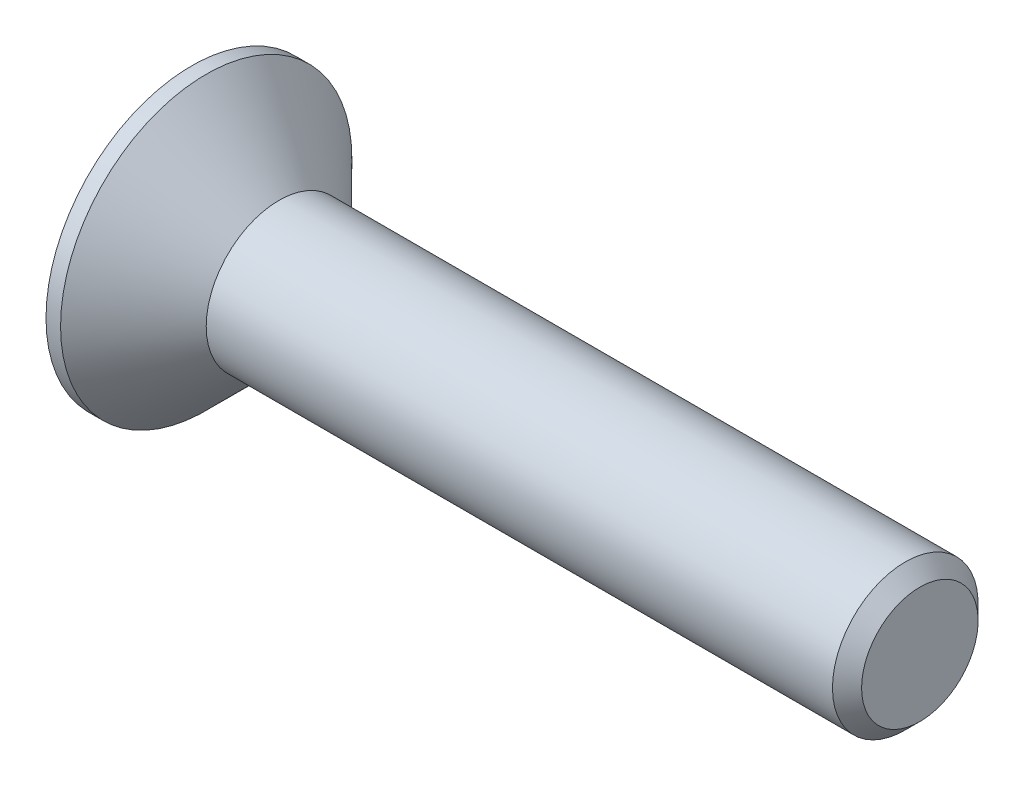
SolidWorks part; units mm, degrees
ref_plane "Front Plane" through (0, 0, 0) normal (0, 0, 1) x (1, 0, 0)
ref_plane "Top Plane" through (0, 0, 0) normal (0, 1, 0) x (1, 0, 0)
ref_plane "Right Plane" through (0, 0, 0) normal (1, 0, 0) x (0, 0, -1)
sketch "Sketch1" plane through (0, 0, 0) normal (0, 0, 1) x (1, 0, 0)
  line L0 (0, 1) -> (-1, 2)
  line L1 (-1, 2) -> (-1.2, 2)
  line L2 (-1.2, 2) -> (-1.2, 0)
  line L3 (-1.2, 0) -> (8.8, 0)
  line L4 (8.8, 0) -> (8.8, 1)
  line L5 (8.8, 1) -> (0, 1)
  dimension "D1" = 1
  dimension "D2" = 10
  dimension "D3" = 45
  dimension "D4" = 2
  dimension "D5" = 1.2
revolve "Revolve1" add sketch "Sketch1" angle 360 about L3
chamfer "Chamfer1" distance 0.2 angle 45 1 edges at (8.8, 0, 1)
sketch "Sketch2" plane through (-1.2, 0, 0) normal (-1, 0, 0) x (0, 0, 1)
  line L1 (-0.7506, 0) -> (-0.3753, -0.65)
  line L2 (-0.3753, -0.65) -> (0.3753, -0.65)
  line L3 (0.3753, -0.65) -> (0.7506, 0)
  line L4 (0.7506, 0) -> (0.3753, 0.65)
  line L5 (0.3753, 0.65) -> (-0.3753, 0.65)
  line L6 (-0.3753, 0.65) -> (-0.7506, 0)
  circle A0 centre (0, 0) radius 0.65 construction
  dimension "D1" = 1.3
extrude "Cut-Extrude1" cut sketch "Sketch2" against normal blind 0.75
